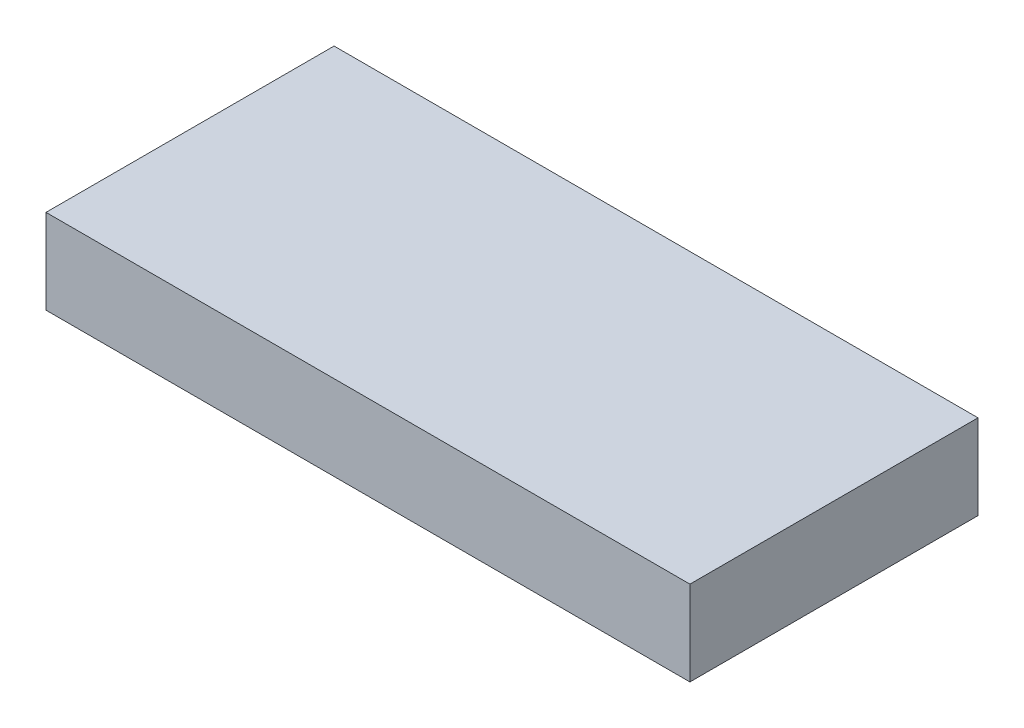
SolidWorks part; units mm, degrees
ref_plane "Front Plane" through (0, 0, 0) normal (0, 0, 1) x (1, 0, 0)
ref_plane "Top Plane" through (0, 0, 0) normal (0, 1, 0) x (1, 0, 0)
ref_plane "Right Plane" through (0, 0, 0) normal (1, 0, 0) x (0, 0, -1)
sketch "Sketch1" plane through (0, 0, 0) normal (0, 1, 0) x (1, 0, 0)
  line L1 (-19, 8.5) -> (19, 8.5)
  line L2 (-19, 8.5) -> (-19, -8.5)
  line L3 (-19, -8.5) -> (19, -8.5)
  line L4 (19, 8.5) -> (19, -8.5)
  line L5 (-19, 8.5) -> (19, -8.5) construction
  line L6 (-19, -8.5) -> (19, 8.5) construction
  point P0 (0, 0)
  dimension "D1" = 17
  dimension "D2" = 38
extrude "Boss-Extrude1" add sketch "Sketch1" along normal blind 5
